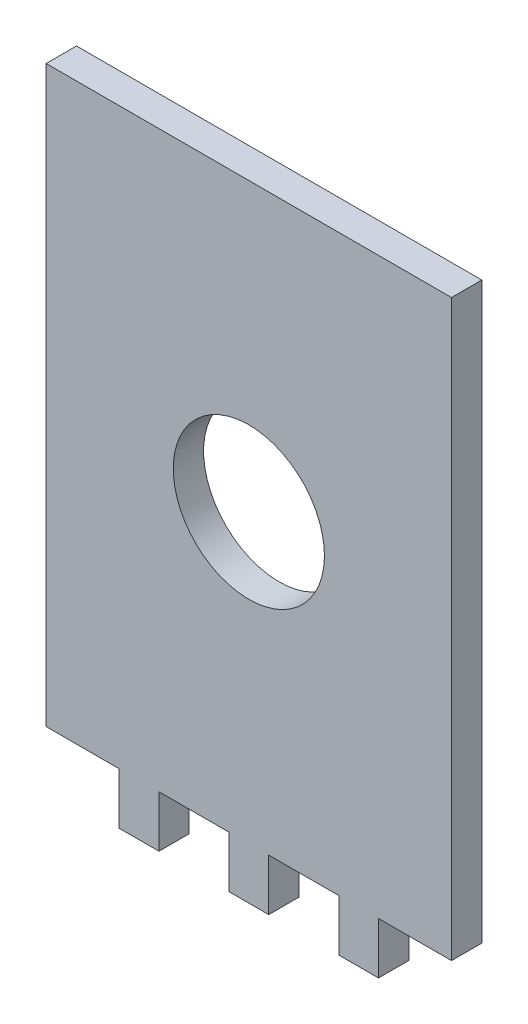
SolidWorks part; units mm, degrees
ref_plane "Front Plane" through (0, 0, 0) normal (0, 0, 1) x (1, 0, 0)
ref_plane "Top Plane" through (0, 0, 0) normal (0, 1, 0) x (1, 0, 0)
ref_plane "Right Plane" through (0, 0, 0) normal (1, 0, 0) x (0, 0, -1)
sketch "Sketch1" plane through (0, 0, 0) normal (0, 0, 1) x (1, 0, 0)
  line L0 (-21.15, 12.3) -> (21.15, 12.3) construction
  line L1 (-21.15, 30) -> (21.15, 30)
  line L2 (-21.15, 30) -> (-21.15, -30)
  line L3 (-21.15, -30) -> (21.15, -30)
  line L4 (21.15, 30) -> (21.15, -30)
  line L5 (2, -35.4) -> (2, -30)
  line L6 (-13.5, -30) -> (-9.5, -30)
  line L7 (-13.5, -30) -> (-13.5, -35.4)
  line L8 (-13.5, -35.4) -> (-9.5, -35.4)
  line L9 (-9.5, -30) -> (-9.5, -35.4)
  line L10 (2, -35.4) -> (-2, -35.4)
  line L11 (2, -30) -> (-2, -30)
  line L12 (-2, -35.4) -> (-2, -30)
  line L13 (2, -35.4) -> (-2, -30) construction
  line L14 (2, -30) -> (-2, -35.4) construction
  line L15 (-21.15, 0) -> (21.15, 0) construction
  line L16 (13.5, -30) -> (9.5, -30)
  line L17 (13.5, -30) -> (13.5, -35.4)
  line L18 (13.5, -35.4) -> (9.5, -35.4)
  line L19 (9.5, -30) -> (9.5, -35.4)
  circle A0 centre (0, 0) radius 8
  point P13 (0, -30)
  point P14 (0, -32.7)
  dimension "D6" = 16
  dimension "D1" = 42.3
  dimension "D3" = 42.3
  dimension "D4" = 30
  dimension "D5" = 21.15
  dimension "D2" = 60
  dimension "D8" = 4
  dimension "D7" = 7.5
  dimension "D10" = 7.5
  dimension "D9" = 5.4
extrude "Boss-Extrude1" add sketch "Sketch1" along normal blind 3.175
sketch "Sketch2" plane through (0, 0, 3.175) normal (0, 0, 1) x (1, 0, 0)
  line L56 (21.1906, -30.0406) -> (21.1906, 30.0406)
  line L57 (21.1906, 30.0406) -> (-21.1906, 30.0406)
  line L70 (-21.1906, 30.0406) -> (-21.1906, -30.0406)
  line L71 (-21.1906, -30.0406) -> (-13.5406, -30.0406)
  line L72 (-13.5406, -30.0406) -> (-13.5406, -35.4406)
  line L73 (-13.5406, -35.4406) -> (-9.4594, -35.4406)
  line L74 (-9.4594, -35.4406) -> (-9.4594, -30.0406)
  line L75 (-9.4594, -30.0406) -> (-2.0406, -30.0406)
  line L76 (-2.0406, -30.0406) -> (-2.0406, -35.4406)
  line L77 (-2.0406, -35.4406) -> (2.0406, -35.4406)
  line L78 (2.0406, -35.4406) -> (2.0406, -30.0406)
  line L79 (2.0406, -30.0406) -> (9.4594, -30.0406)
  line L80 (9.4594, -30.0406) -> (9.4594, -35.4406)
  line L81 (9.4594, -35.4406) -> (13.5406, -35.4406)
  line L82 (13.5406, -35.4406) -> (13.5406, -30.0406)
  line L83 (13.5406, -30.0406) -> (21.1906, -30.0406)
  line L84 (21.1906, -30.0406) -> (21.1906, 30.0406)
  line L85 (21.1906, 30.0406) -> (-21.1906, 30.0406)
  line L98 (-21.1906, 30.0406) -> (-21.1906, -30.0406)
  line L99 (-21.1906, -30.0406) -> (-13.5406, -30.0406)
  line L100 (-13.5406, -30.0406) -> (-13.5406, -35.4406)
  line L101 (-13.5406, -35.4406) -> (-9.4594, -35.4406)
  line L102 (-9.4594, -35.4406) -> (-9.4594, -30.0406)
  line L103 (-9.4594, -30.0406) -> (-2.0406, -30.0406)
  line L104 (-2.0406, -30.0406) -> (-2.0406, -35.4406)
  line L105 (-2.0406, -35.4406) -> (2.0406, -35.4406)
  line L106 (2.0406, -35.4406) -> (2.0406, -30.0406)
  line L107 (2.0406, -30.0406) -> (9.4594, -30.0406)
  line L108 (9.4594, -30.0406) -> (9.4594, -35.4406)
  line L109 (9.4594, -35.4406) -> (13.5406, -35.4406)
  line L110 (13.5406, -35.4406) -> (13.5406, -30.0406)
  line L111 (13.5406, -30.0406) -> (21.1906, -30.0406)
  circle A2 centre (0, 0) radius 7.9594
  circle A3 centre (0, 0) radius 7.9594
  dimension "D1" = 0.0406
  dimension "D2" = 0.0406
extrude "Boss-Extrude3" add sketch "Sketch2" against normal blind 3.175
sketch "Sketch3" plane through (0, 0, 3.175) normal (0, 0, 1) x (1, 0, 0)
  line L32 (-21.2313, 30.0813) -> (-21.2313, -30.0813)
  line L33 (-21.2313, -30.0813) -> (-13.5813, -30.0813)
  line L34 (-13.5813, -30.0813) -> (-13.5813, -35.4813)
  line L35 (-13.5813, -35.4813) -> (-9.4187, -35.4813)
  line L36 (-9.4187, -35.4813) -> (-9.4187, -30.0813)
  line L37 (-9.4187, -30.0813) -> (-2.0813, -30.0813)
  line L38 (-2.0813, -30.0813) -> (-2.0813, -35.4813)
  line L39 (-2.0813, -35.4813) -> (2.0813, -35.4813)
  line L40 (2.0813, -35.4813) -> (2.0813, -30.0813)
  line L41 (2.0813, -30.0813) -> (9.4187, -30.0813)
  line L42 (9.4187, -30.0813) -> (9.4187, -35.4813)
  line L43 (9.4187, -35.4813) -> (13.5813, -35.4813)
  line L44 (13.5813, -35.4813) -> (13.5813, -30.0813)
  line L45 (13.5813, -30.0813) -> (21.2313, -30.0813)
  line L46 (21.2313, -30.0813) -> (21.2313, 30.0813)
  line L47 (21.2313, 30.0813) -> (-21.2313, 30.0813)
  line L48 (-21.2313, 30.0813) -> (-21.2313, -30.0813)
  line L49 (-21.2313, -30.0813) -> (-13.5813, -30.0813)
  line L50 (-13.5813, -30.0813) -> (-13.5813, -35.4813)
  line L51 (-13.5813, -35.4813) -> (-9.4187, -35.4813)
  line L52 (-9.4187, -35.4813) -> (-9.4187, -30.0813)
  line L53 (-9.4187, -30.0813) -> (-2.0813, -30.0813)
  line L54 (-2.0813, -30.0813) -> (-2.0813, -35.4813)
  line L55 (-2.0813, -35.4813) -> (2.0813, -35.4813)
  line L56 (2.0813, -35.4813) -> (2.0813, -30.0813)
  line L57 (2.0813, -30.0813) -> (9.4187, -30.0813)
  line L58 (9.4187, -30.0813) -> (9.4187, -35.4813)
  line L59 (9.4187, -35.4813) -> (13.5813, -35.4813)
  line L60 (13.5813, -35.4813) -> (13.5813, -30.0813)
  line L61 (13.5813, -30.0813) -> (21.2313, -30.0813)
  line L62 (21.2313, -30.0813) -> (21.2313, 30.0813)
  line L63 (21.2313, 30.0813) -> (-21.2313, 30.0813)
  circle A2 centre (0, 0) radius 7.9187
  circle A4 centre (0, 0) radius 7.9187
  dimension "D1" = 0.0406
  dimension "D2" = 0.0406
extrude "Boss-Extrude4" add sketch "Sketch3" against normal up to surface (3.175 mm away) up to face at (0, -24.5555, 0)
equation "\"stepper width\"=4.23"
equation "\"stepper hole disctance\"= 3.1"
equation "\"stepper hole diameter\"=0.34"
equation "\"stepper shaft hole\"=2.4"
equation "\"tooth width\"=0.4"
equation "\"tooth thickness\"=0.3175"
equation "\"tooth to side\"=0.75"
equation "\"motor chamber height\"= 6"
equation "\"D1@Sketch1\"=\"stepper width\""
equation "\"D3@Sketch1\"=\"stepper width\""
equation "\"D5@Sketch1\"=\"stepper width\"/2"
equation "\"gear shaft diameter\"=1.6"
equation "\"D6@Sketch1\"=\"gear shaft diameter\""
equation "\"D2@Sketch1\"=\"motor chamber height\""
equation "\"D8@Sketch1\"=\"tooth width\""
equation "\"D1@Boss-Extrude1\"=\"tooth thickness\""
equation "\"D7@Sketch1\"=.75"
equation "\"D10@Sketch1\"=.75"
equation "\"D5@Sketch1\"=\"stepper hole diameter\""
